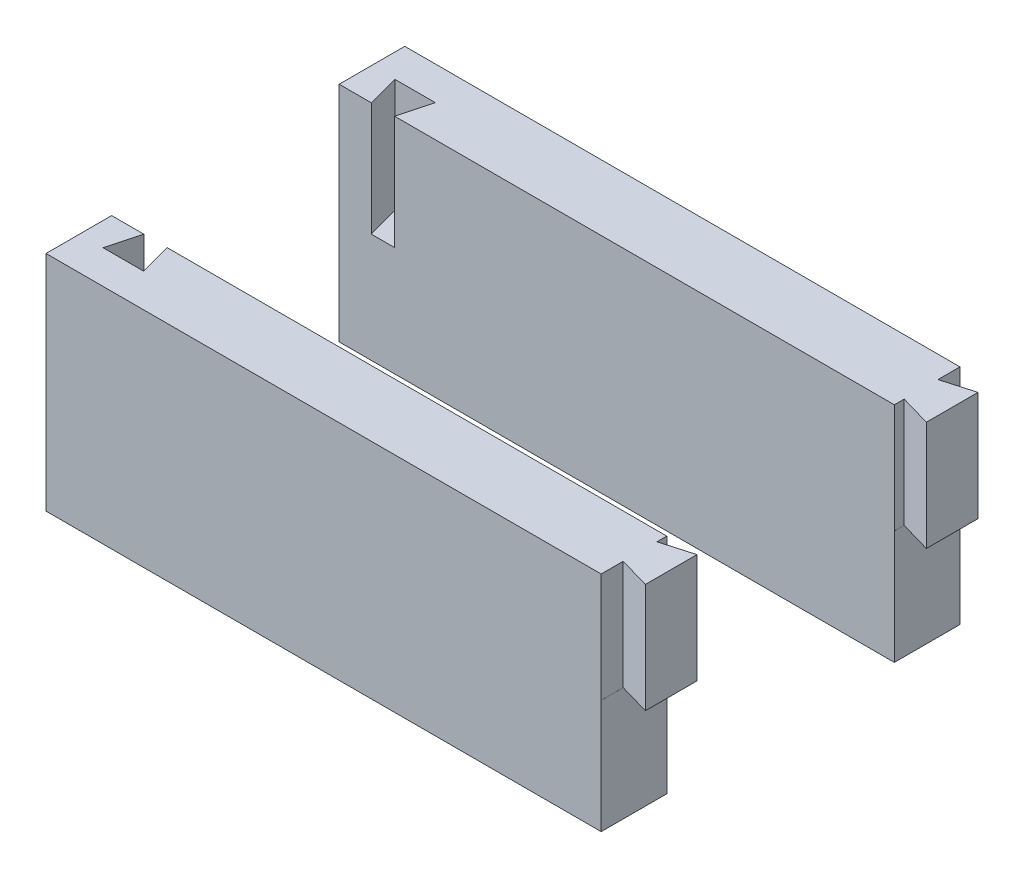
SolidWorks part; units mm, degrees
ref_plane "Front Plane" through (0, 0, 0) normal (0, 0, 1) x (1, 0, 0)
ref_plane "Top Plane" through (0, 0, 0) normal (0, 1, 0) x (1, 0, 0)
ref_plane "Right Plane" through (0, 0, 0) normal (1, 0, 0) x (0, 0, -1)
sketch "Sketch1" plane through (0, 0, 0) normal (0, 0, 1) x (1, 0, 0)
  line L1 (-60.9366, 28.6127) -> (73.0634, 28.6127)
  line L2 (-60.9366, 28.6127) -> (-60.9366, -22.3873)
  line L3 (-60.9366, -22.3873) -> (73.0634, -22.3873)
  line L4 (73.0634, 28.6127) -> (73.0634, -22.3873)
  dimension "D1" = 51
  dimension "D2" = 134
extrude "Boss-Extrude1" add sketch "Sketch1" along normal blind 15
sketch "Sketch3" plane through (0, 28.6127, 0) normal (0, 1, 0) x (1, 0, 0)
  line L0 (-60.9366, 0) -> (-53.5866, 0)
  line L2 (73.0634, 0) -> (-60.9366, 0) construction
  line L3 (-53.5866, 0) -> (-55.5536, -7.341)
  line L4 (-55.5536, -7.341) -> (-46.3196, -7.341)
  line L5 (-46.3196, -7.341) -> (-48.2866, 0)
  dimension "D1" = 7.35
  dimension "D2" = 105
  dimension "D3" = 105
  dimension "D4" = 75
  dimension "D5" = 75
  dimension "D6" = 7.6
  dimension "D7" = 7.6
  dimension "D8" = 5.3
  dimension "D9" = 9.234
extrude "Cut-Extrude2" cut sketch "Sketch3" against normal blind 26 and the other way through all
sketch "Sketch5" plane through (0, 28.6127, 0) normal (0, 1, 0) x (1, 0, 0)
  line L3 (65.95, 0) -> (73.0634, 0)
  line L4 (73.0634, 0) -> (-48.2866, 0) construction
  line L5 (73.0634, 0) -> (73.0634, -0.2103)
  line L6 (73.0634, -15) -> (73.0634, 0) construction
  line L7 (73.0634, -0.2103) -> (65.95, -2.25)
  line L8 (65.95, -2.25) -> (65.95, 0)
  line L9 (65.95, -15) -> (65.95, -9.9706)
  line L10 (73.0634, -15) -> (-60.9366, -15) construction
  line L11 (65.95, -9.9706) -> (73.0634, -12.0103)
  line L12 (73.0634, -12.0103) -> (73.0634, -15)
  line L13 (73.0634, -15) -> (65.95, -15)
  dimension "D1" = 7.4
  dimension "D2" = 7.4
  dimension "D3" = 106
  dimension "D4" = 7.1133
  dimension "D5" = 11.8
  dimension "D6" = 2.25
extrude "Cut-Extrude4" cut sketch "Sketch5" against normal blind 25
sketch "Sketch7" plane through (0, -22.3873, 0) normal (0, -1, 0) x (1, 0, 0)
  line L0 (-60.9366, 0) -> (73.0634, 0) construction
  line L1 (65.9534, 0) -> (73.0634, 0)
  line L2 (65.9534, 0) -> (65.9534, 15)
  line L3 (65.9534, 15) -> (73.0634, 15)
  line L4 (73.0634, 0) -> (73.0634, 15)
  dimension "D1" = 7.11
extrude "Cut-Extrude5" cut sketch "Sketch7" against normal blind 26
ref_plane "Plane3" through (0, 0, -26) normal (0, 0, -1) x (-1, 0, 0)
mirror "Mirror2" about plane through (0, 0, -26) normal (0, 0, -1) of bodies 107
